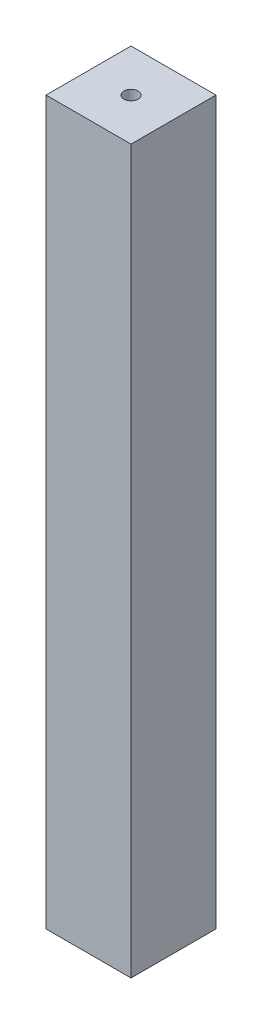
SolidWorks part; units mm, degrees
ref_plane "Front Plane" through (0, 0, 0) normal (0, 0, 1) x (1, 0, 0)
ref_plane "Top Plane" through (0, 0, 0) normal (0, 1, 0) x (1, 0, 0)
ref_plane "Right Plane" through (0, 0, 0) normal (1, 0, 0) x (0, 0, -1)
sketch "Sketch1" plane through (0, 0, 0) normal (0, 1, 0) x (1, 0, 0)
  line L0 (5, 5) -> (5, 25)
  line L1 (0, 0) -> (30, 0)
  line L2 (0, 0) -> (0, 30)
  line L3 (0, 30) -> (30, 30)
  line L4 (30, 0) -> (30, 30)
  line L5 (5, 25) -> (25, 25)
  line L6 (25, 5) -> (25, 25)
  line L7 (5, 5) -> (25, 5)
  dimension "D1" = 30
  dimension "D2" = 30
  dimension "D3" = 5
extrude "Boss-Extrude1" add sketch "Sketch1" along normal blind 250
sketch "Sketch2" plane through (0, 250, 0) normal (0, 1, 0) x (1, 0, 0)
  line L4 (0, 30) -> (0, 0)
  line L5 (0, 0) -> (30, 0)
  line L6 (30, 0) -> (30, 30)
  line L7 (30, 30) -> (0, 30)
  line L8 (0, 30) -> (0, 0)
  line L9 (0, 0) -> (30, 0)
  line L10 (30, 0) -> (30, 30)
  line L11 (30, 30) -> (0, 30)
  circle A0 centre (15, 15) radius 2.5
  point P7 (0, 15)
  point P8 (15, 30)
  dimension "D2" = 5
  dimension "D1" = 0
extrude "Boss-Extrude2" add sketch "Sketch2" along normal blind 5
